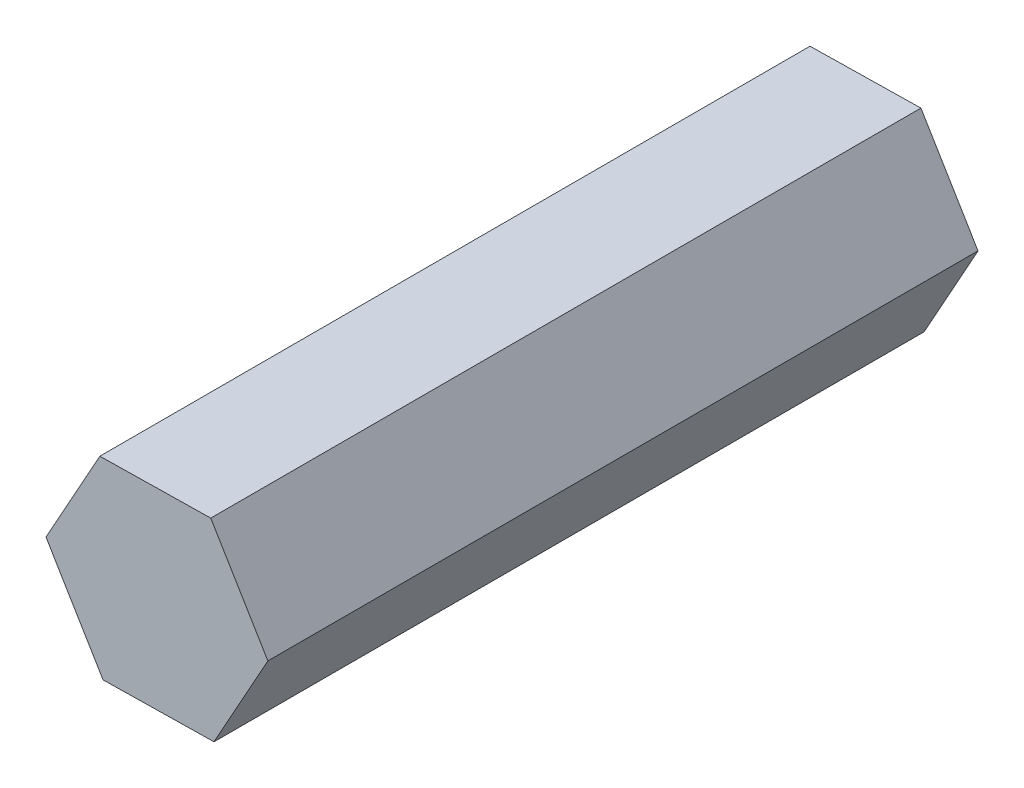
SolidWorks part; units mm, degrees
ref_plane "前视基准面" through (0, 0, 0) normal (0, 0, 1) x (1, 0, 0)
ref_plane "上视基准面" through (0, 0, 0) normal (0, 1, 0) x (1, 0, 0)
ref_plane "右视基准面" through (0, 0, 0) normal (1, 0, 0) x (0, 0, -1)
other "Configuration Table"
sketch "草图1" plane through (0, 0, 0) normal (0, 0, 1) x (1, 0, 0)
  line L1 (-2.6543, 24.5611) -> (-1.3653, 26.8831)
  line L2 (-1.3653, 26.8831) -> (-2.7317, 29.1604)
  line L3 (-2.7317, 29.1604) -> (-5.3871, 29.1158)
  line L4 (-5.3871, 29.1158) -> (-6.6761, 26.7938)
  line L5 (-6.6761, 26.7938) -> (-5.3097, 24.5164)
  line L6 (-5.3097, 24.5164) -> (-2.6543, 24.5611)
  circle A0 centre (-4.0207, 26.8384) radius 2.3 construction
  dimension "D1" = 4.6
extrude "凸台-拉伸1" add sketch "草图1" along normal blind 17
